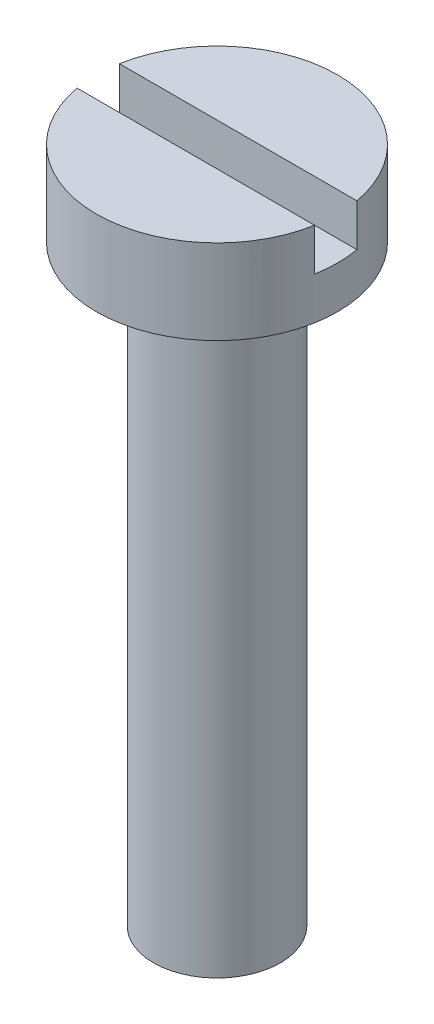
SolidWorks part; units mm, degrees
material "1023 Carbon Steel Sheet (SS)"
ref_plane "Front Plane" through (0, 0, 0) normal (0, 0, 1) x (1, 0, 0)
ref_plane "Top Plane" through (0, 0, 0) normal (0, 1, 0) x (1, 0, 0)
ref_plane "Right Plane" through (0, 0, 0) normal (1, 0, 0) x (0, 0, -1)
sketch "Sketch1" plane through (0, 0, 0) normal (0, 1, 0) x (1, 0, 0)
  circle A0 centre (0, 0) radius 2.85
  dimension "D1" = 5.7
extrude "Boss-Extrude1" add sketch "Sketch1" along normal blind 2
sketch "Sketch2" plane through (0, 0, 0) normal (0, 1, 0) x (1, 0, 0)
  circle A0 centre (0, 0) radius 1.5
  dimension "D1" = 3
extrude "Boss-Extrude2" add sketch "Sketch2" against normal blind 14
sketch "Sketch3" plane through (0, 2, 0) normal (0, 1, 0) x (1, 0, 0)
  line L1 (-3, -0.5) -> (3, -0.5)
  line L2 (-3, -0.5) -> (-3, 0.5)
  line L3 (-3, 0.5) -> (3, 0.5)
  line L4 (3, -0.5) -> (3, 0.5)
  line L5 (-3, -0.5) -> (3, 0.5) construction
  line L6 (-3, 0.5) -> (3, -0.5) construction
  point P0 (0, 0)
  dimension "D1" = 1
  dimension "D2" = 6
extrude "Cut-Extrude1" cut sketch "Sketch3" against normal blind 1
